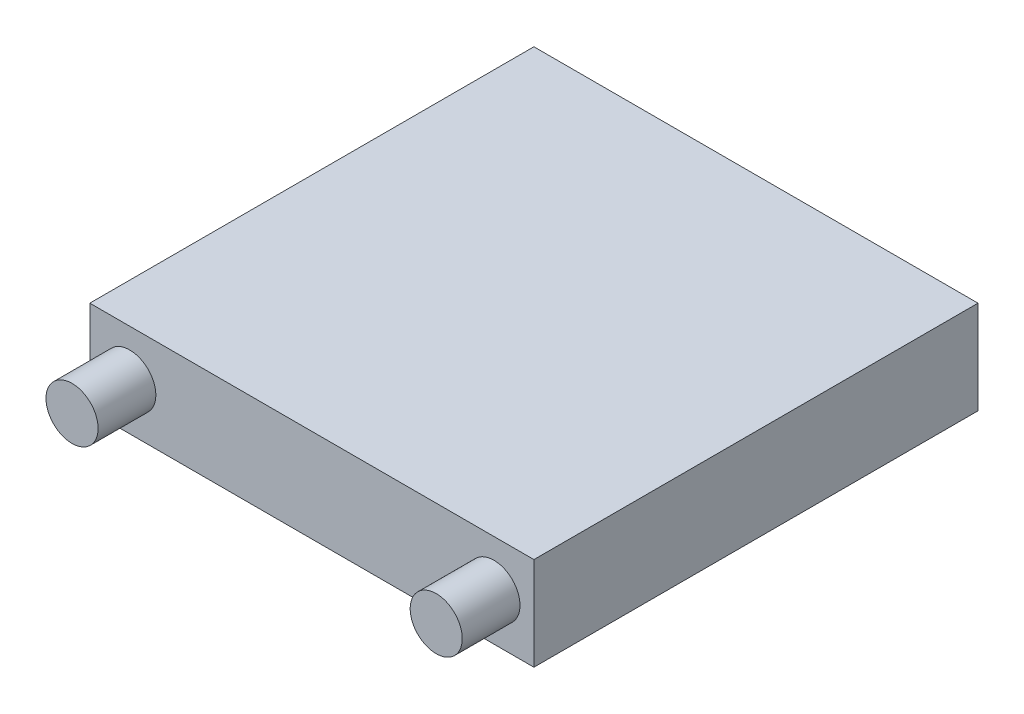
SolidWorks part; units mm, degrees
ref_plane "前视基准面" through (0, 0, 0) normal (0, 0, 1) x (1, 0, 0)
ref_plane "上视基准面" through (0, 0, 0) normal (0, 1, 0) x (1, 0, 0)
ref_plane "右视基准面" through (0, 0, 0) normal (1, 0, 0) x (0, 0, -1)
sketch "草图1" plane through (0, 0, 0) normal (0, 1, 0) x (1, 0, 0)
  line L1 (-10, 10) -> (10, 10)
  line L2 (-10, 10) -> (-10, -10)
  line L3 (-10, -10) -> (10, -10)
  line L4 (10, 10) -> (10, -10)
  line L5 (-10, 10) -> (10, -10) construction
  line L6 (-10, -10) -> (10, 10) construction
  point P0 (0, 0)
  dimension "D1" = 20
  dimension "D2" = 20
extrude "凸台-拉伸1" add sketch "草图1" along normal blind 4.2
sketch "草图2" plane through (0, 0, 0) normal (0, 0, 1) x (1, 0, 0)
  line L0 (0, 5.2132) -> (0, -1.0709) construction
  line L1 (-10, 4.2) -> (10, 4.2) construction
  circle A0 centre (-8.2, 2.1) radius 1.1731
  circle A1 centre (8.2, 2.1) radius 1.1731
  dimension "D1" = 8.2
  dimension "D2" = 2.1
extrude "凸台-拉伸2" add sketch "草图2" along normal blind 12.6
